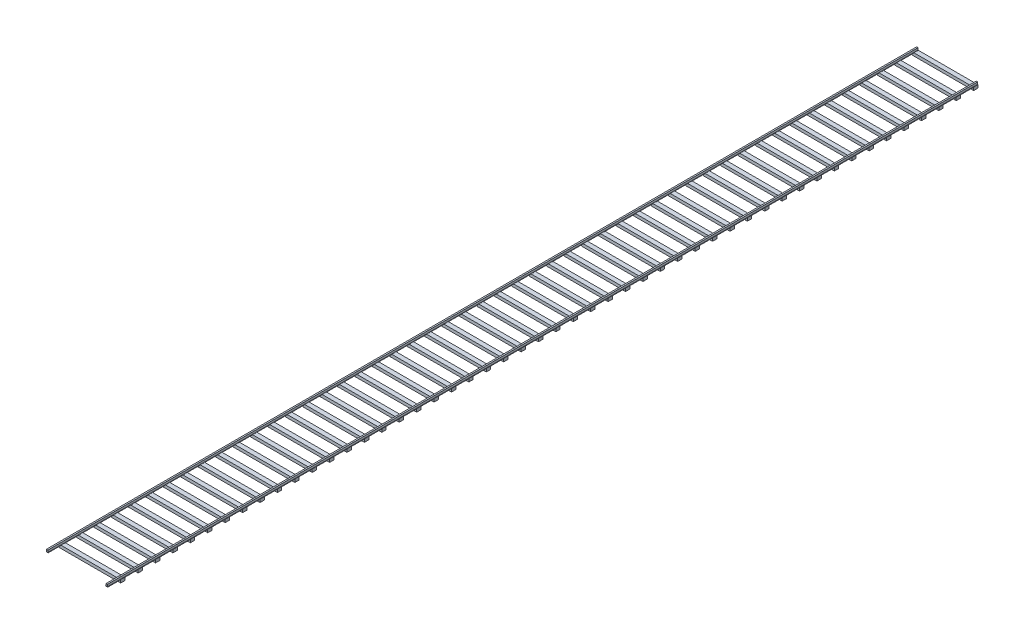
SolidWorks part; units mm, degrees
ref_plane "Front Plane" through (0, 0, 0) normal (0, 0, 1) x (1, 0, 0)
ref_plane "Top Plane" through (0, 0, 0) normal (0, 1, 0) x (1, 0, 0)
ref_plane "Right Plane" through (0, 0, 0) normal (1, 0, 0) x (0, 0, -1)
sketch "Sketch1" plane through (0, 0, 0) normal (0, 0, 1) x (1, 0, 0)
  line L0 (1988.4942, 32.5663) -> (1988.4942, 36.8424)
  line L1 (1988.4942, 36.8424) -> (2001.1942, 36.8424)
  line L2 (2001.1942, 36.8424) -> (2001.1942, 110.9137)
  line L3 (2001.1942, 110.9137) -> (2051.9942, 110.9137)
  line L4 (2051.9942, 110.9137) -> (2051.9942, 36.8424)
  line L5 (2051.9942, 36.8424) -> (2064.6942, 36.8424)
  line L6 (2064.6942, 36.8424) -> (2064.6942, 32.5663)
  line L7 (2064.6942, 32.5663) -> (1988.4942, 32.5663)
  line L8 (-81.6058, 110.9137) -> (-30.8058, 110.9137)
  line L9 (-30.8058, 110.9137) -> (-30.8058, 36.8424)
  line L10 (-30.8058, 36.8424) -> (-18.1058, 36.8424)
  line L11 (-18.1058, 36.8424) -> (-18.1058, 34.7137)
  line L12 (-18.1058, 34.7137) -> (-94.3058, 34.7137)
  line L13 (-94.3058, 34.7137) -> (-94.3058, 36.8424)
  line L14 (-94.3058, 36.8424) -> (-81.6058, 36.8424)
  line L15 (-81.6058, 36.8424) -> (-81.6058, 110.9137)
  line L16 (-56.2058, 34.7137) -> (-56.2058, 110.9137) construction
  line L17 (2026.5942, 110.9137) -> (2026.5942, 32.5663) construction
  line L18 (-30.8058, 110.9137) -> (2001.1942, 110.9137) construction
  line L19 (-81.6058, 36.8424) -> (-30.8058, 36.8424) construction
  line L20 (-18.1058, 36.8424) -> (1988.4942, 36.8424) construction
  line L21 (2001.1942, 36.8424) -> (2051.9942, 36.8424) construction
  dimension "D1" = 76.2
  dimension "D2" = 76.2
  dimension "D3" = 50.8
  dimension "D4" = 50.8
  dimension "D5" = 76.2
  dimension "D6" = 2032
extrude "Boss-Extrude1" add sketch "Sketch1" along normal blind 30480
sketch "Sketch2" plane through (0, 32.5663, 0) normal (0, -1, 0) x (1, 0, 0)
  line L0 (2064.6942, 30480) -> (2064.6942, 0) construction
  line L1 (-94.3058, 0) -> (2064.6942, 0)
  line L2 (-94.3058, 0) -> (-94.3058, 152.4)
  line L3 (-94.3058, 152.4) -> (2064.6942, 152.4)
  line L4 (2064.6942, 0) -> (2064.6942, 152.4)
  dimension "D1" = 152.4
extrude "Boss-Extrude3" add sketch "Sketch2" along normal blind 101.6
pattern_linear "LPattern1" count 50 spacing 609.6 along (0, 0, 1) of "Boss-Extrude3"
